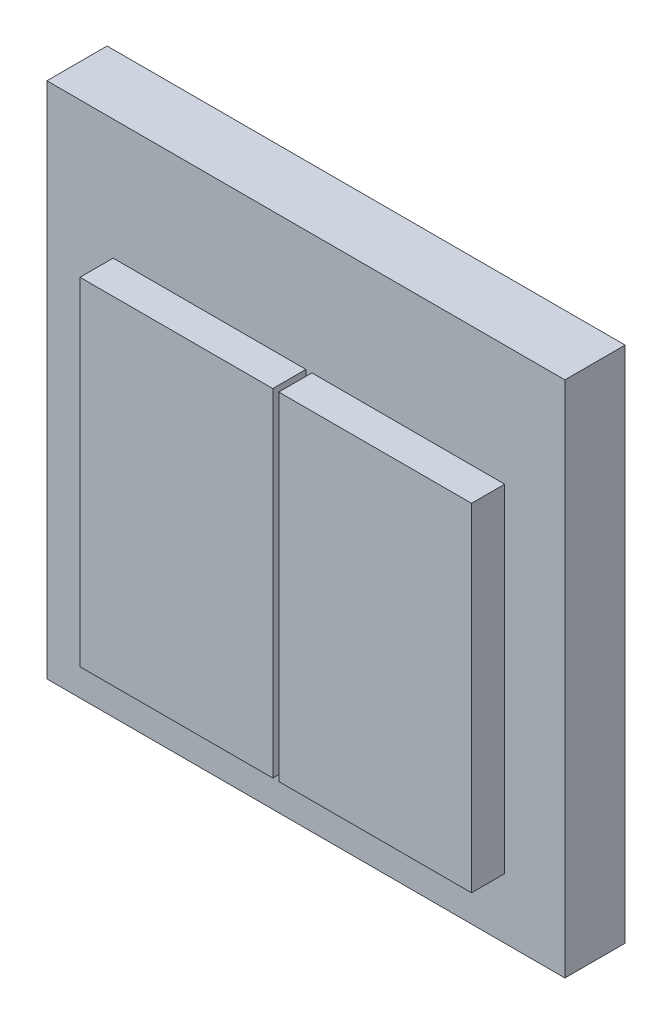
SolidWorks part; units mm, degrees
ref_plane "前视基准面" through (0, 0, 0) normal (0, 0, 1) x (1, 0, 0)
ref_plane "上视基准面" through (0, 0, 0) normal (0, 1, 0) x (1, 0, 0)
ref_plane "右视基准面" through (0, 0, 0) normal (1, 0, 0) x (0, 0, -1)
sketch "草图1" plane through (0, 0, 0) normal (0, 0, 1) x (1, 0, 0)
  line L1 (-43, 43) -> (43, 43)
  line L2 (-43, 43) -> (-43, -43)
  line L3 (-43, -43) -> (43, -43)
  line L4 (43, 43) -> (43, -43)
  line L5 (0, -43) -> (0, 43) construction
  line L6 (-43, 0) -> (43, 0) construction
  point P76 (0, 0)
extrude "凸台-拉伸2" add sketch "草图1" against normal up to surface (10 mm away) separate body
sketch "草图2" plane through (0, 0, 0) normal (0, 0, 1) x (1, 0, 0)
  line L1 (33, -33) -> (1, -33)
  line L2 (33, -33) -> (33, 23)
  line L3 (33, 23) -> (1, 23)
  line L4 (-32, -33) -> (-32, 23)
  line L5 (33, -33) -> (-32, 23) construction
  line L6 (33, 23) -> (-32, -33) construction
  line L7 (-43, 43) -> (-43, -43) construction
  line L8 (43, 43) -> (-43, 43) construction
  line L9 (0.5, 23) -> (0.5, -33) construction
  line L10 (0, 23) -> (0, -33)
  line L11 (1, 23) -> (1, -33)
  line L14 (0, 23) -> (-32, 23)
  line L15 (0, -33) -> (-32, -33)
  point P0 (0, 0)
  dimension "D1" = 65
  dimension "D2" = 56
  dimension "D3" = 11
  dimension "D4" = 20
  dimension "D5" = 0.5
  dimension "D6" = 0.5
extrude "凸台-拉伸3" add sketch "草图2" along normal blind 5.5
